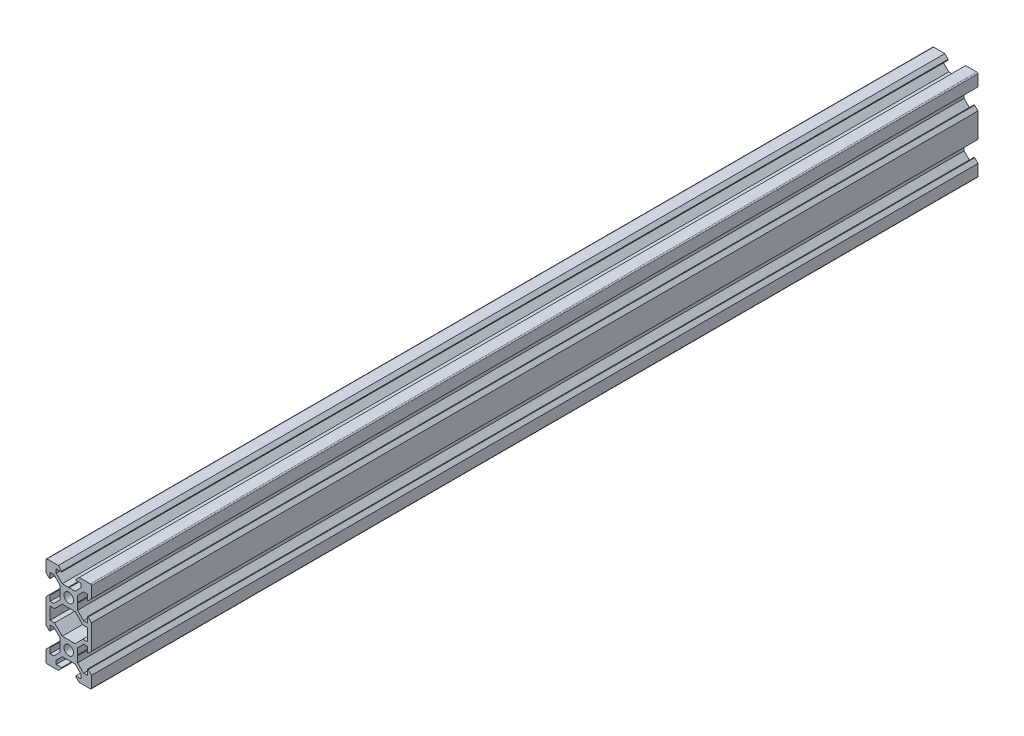
SolidWorks part; units mm, degrees
material "6061-T6 (SS)"
ref_plane "Front Plane" through (0, 0, 0) normal (0, 0, 1) x (1, 0, 0)
ref_plane "Top Plane" through (0, 0, 0) normal (0, 1, 0) x (1, 0, 0)
ref_plane "Right Plane" through (0, 0, 0) normal (1, 0, 0) x (0, 0, -1)
sketch "Sketch1" plane through (0, 0, 0) normal (0, 0, 1) x (1, 0, 0)
  line L0 (0, 0) -> (10, 0) construction
  line L1 (9.5, -20) -> (-9.5, -20)
  line L2 (10, -19.5) -> (10, 19.5)
  line L3 (9.5, 20) -> (-9.5, 20)
  line L4 (-10, -19.5) -> (-10, 19.5)
  line L5 (10, -20) -> (-10, 20) construction
  line L6 (10, 20) -> (-10, -20) construction
  circle A0 centre (0, 10) radius 2.1
  circle A1 centre (0, -10) radius 2.1
  arc A2 (-9.5, -20) -> (-10, -19.5) centre (-9.5, -19.5) cw
  arc A3 (9.5, -20) -> (10, -19.5) centre (9.5, -19.5) ccw
  arc A4 (10, 19.5) -> (9.5, 20) centre (9.5, 19.5) ccw
  arc A5 (-9.5, 20) -> (-10, 19.5) centre (-9.5, 19.5) ccw
  point P0 (0, 0)
  line B0 (0, 10) -> (0, 20) construction
  line B1 (0, 13.69) -> (-0.21, 13.9)
  line B2 (-0.21, 13.9) -> (-2.8393, 13.9)
  line B3 (-2.8393, 13.9) -> (-5.5, 16.5607)
  line B4 (-5.5, 16.5607) -> (-5.5, 18.2)
  line B5 (-5.5, 18.2) -> (-3.125, 18.2)
  line B6 (-3.125, 18.2) -> (-3.125, 18.545)
  line B7 (-3.125, 18.545) -> (-4.58, 20)
  line B8 (-4.58, 20) -> (4.58, 20)
  line B9 (0, 10) -> (-5.9132, 15.9132) construction
  line B10 (3.125, 18.545) -> (4.58, 20)
  line B11 (3.125, 18.2) -> (3.125, 18.545)
  line B12 (5.5, 18.2) -> (3.125, 18.2)
  line B13 (5.5, 16.5607) -> (5.5, 18.2)
  line B14 (2.8393, 13.9) -> (5.5, 16.5607)
  line B15 (0.21, 13.9) -> (2.8393, 13.9)
  line B16 (0, 13.69) -> (0.21, 13.9)
  line B17 (0, 10) -> (-10, 10) construction
  line B18 (-3.69, 10) -> (-3.9, 9.79)
  line B19 (-3.9, 9.79) -> (-3.9, 7.1607)
  line B20 (-3.9, 7.1607) -> (-6.5607, 4.5)
  line B21 (-6.5607, 4.5) -> (-8.2, 4.5)
  line B22 (-8.2, 4.5) -> (-8.2, 6.875)
  line B23 (-8.2, 6.875) -> (-8.545, 6.875)
  line B24 (-8.545, 6.875) -> (-10, 5.42)
  line B25 (-10, 5.42) -> (-10, 14.58)
  line B26 (0, 10) -> (-5.9132, 4.0868) construction
  line B27 (-8.545, 13.125) -> (-10, 14.58)
  line B28 (-8.2, 13.125) -> (-8.545, 13.125)
  line B29 (-8.2, 15.5) -> (-8.2, 13.125)
  line B30 (-6.5607, 15.5) -> (-8.2, 15.5)
  line B31 (-3.9, 12.8393) -> (-6.5607, 15.5)
  line B32 (-3.9, 10.21) -> (-3.9, 12.8393)
  line B33 (-3.69, 10) -> (-3.9, 10.21)
  line B34 (0, -10) -> (-10, -10) construction
  line B35 (-3.69, -10) -> (-3.9, -10.21)
  line B36 (-3.9, -10.21) -> (-3.9, -12.8393)
  line B37 (-3.9, -12.8393) -> (-6.5607, -15.5)
  line B38 (-6.5607, -15.5) -> (-8.2, -15.5)
  line B39 (-8.2, -15.5) -> (-8.2, -13.125)
  line B40 (-8.2, -13.125) -> (-8.545, -13.125)
  line B41 (-8.545, -13.125) -> (-10, -14.58)
  line B42 (-10, -14.58) -> (-10, -5.42)
  line B43 (0, -10) -> (-5.9132, -15.9132) construction
  line B44 (-8.545, -6.875) -> (-10, -5.42)
  line B45 (-8.2, -6.875) -> (-8.545, -6.875)
  line B46 (-8.2, -4.5) -> (-8.2, -6.875)
  line B47 (-6.5607, -4.5) -> (-8.2, -4.5)
  line B48 (-3.9, -7.1607) -> (-6.5607, -4.5)
  line B49 (-3.9, -9.79) -> (-3.9, -7.1607)
  line B50 (-3.69, -10) -> (-3.9, -9.79)
  line B51 (0, -10) -> (0, -20) construction
  line B52 (0, -13.69) -> (0.21, -13.9)
  line B53 (0.21, -13.9) -> (2.8393, -13.9)
  line B54 (2.8393, -13.9) -> (5.5, -16.5607)
  line B55 (5.5, -16.5607) -> (5.5, -18.2)
  line B56 (5.5, -18.2) -> (3.125, -18.2)
  line B57 (3.125, -18.2) -> (3.125, -18.545)
  line B58 (3.125, -18.545) -> (4.58, -20)
  line B59 (4.58, -20) -> (-4.58, -20)
  line B60 (0, -10) -> (5.9132, -15.9132) construction
  line B61 (-3.125, -18.545) -> (-4.58, -20)
  line B62 (-3.125, -18.2) -> (-3.125, -18.545)
  line B63 (-5.5, -18.2) -> (-3.125, -18.2)
  line B64 (-5.5, -16.5607) -> (-5.5, -18.2)
  line B65 (-2.8393, -13.9) -> (-5.5, -16.5607)
  line B66 (-0.21, -13.9) -> (-2.8393, -13.9)
  line B67 (0, -13.69) -> (-0.21, -13.9)
  line B68 (0, -10) -> (10, -10) construction
  line B69 (3.69, -10) -> (3.9, -9.79)
  line B70 (3.9, -9.79) -> (3.9, -7.1607)
  line B71 (3.9, -7.1607) -> (6.5607, -4.5)
  line B72 (6.5607, -4.5) -> (8.2, -4.5)
  line B73 (8.2, -4.5) -> (8.2, -6.875)
  line B74 (8.2, -6.875) -> (8.545, -6.875)
  line B75 (8.545, -6.875) -> (10, -5.42)
  line B76 (10, -5.42) -> (10, -14.58)
  line B77 (0, -10) -> (5.9132, -4.0868) construction
  line B78 (8.545, -13.125) -> (10, -14.58)
  line B79 (8.2, -13.125) -> (8.545, -13.125)
  line B80 (8.2, -15.5) -> (8.2, -13.125)
  line B81 (6.5607, -15.5) -> (8.2, -15.5)
  line B82 (3.9, -12.8393) -> (6.5607, -15.5)
  line B83 (3.9, -10.21) -> (3.9, -12.8393)
  line B84 (3.69, -10) -> (3.9, -10.21)
  line B85 (0, 10) -> (10, 10) construction
  line B86 (3.69, 10) -> (3.9, 10.21)
  line B87 (3.9, 10.21) -> (3.9, 12.8393)
  line B88 (3.9, 12.8393) -> (6.5607, 15.5)
  line B89 (6.5607, 15.5) -> (8.2, 15.5)
  line B90 (8.2, 15.5) -> (8.2, 13.125)
  line B91 (8.2, 13.125) -> (8.545, 13.125)
  line B92 (8.545, 13.125) -> (10, 14.58)
  line B93 (10, 14.58) -> (10, 5.42)
  line B94 (0, 10) -> (5.9132, 15.9132) construction
  line B95 (8.545, 6.875) -> (10, 5.42)
  line B96 (8.2, 6.875) -> (8.545, 6.875)
  line B97 (8.2, 4.5) -> (8.2, 6.875)
  line B98 (6.5607, 4.5) -> (8.2, 4.5)
  line B99 (3.9, 7.1607) -> (6.5607, 4.5)
  line B100 (3.9, 9.79) -> (3.9, 7.1607)
  line B101 (3.69, 10) -> (3.9, 9.79)
  line B102 (-8.2, -2.7) -> (-8.2, 2.7)
  line B103 (-8.2, 2.7) -> (-6.2393, 2.7)
  line B104 (-6.2393, 2.7) -> (-2.8393, 6.1)
  line B105 (-2.8393, 6.1) -> (2.8393, 6.1)
  line B106 (0, 6.1) -> (0, 0) construction
  line B107 (0, 0) -> (-8.2, 0) construction
  line B108 (6.2393, 2.7) -> (2.8393, 6.1)
  line B109 (8.2, 2.7) -> (6.2393, 2.7)
  line B110 (8.2, -2.7) -> (8.2, 2.7)
  line B111 (8.2, -2.7) -> (6.2393, -2.7)
  line B112 (6.2393, -2.7) -> (2.8393, -6.1)
  line B113 (-2.8393, -6.1) -> (2.8393, -6.1)
  line B114 (-6.2393, -2.7) -> (-2.8393, -6.1)
  line B115 (-8.2, -2.7) -> (-6.2393, -2.7)
  line B116 (0, 6.1) -> (0, 10) construction
  line B117 (0, 10) -> (-5.0927, 4.9073) construction
  dimension "D4" = 4.2
  dimension "D5" = 0.5
  dimension "D1" = 20
  dimension "D2" = 40
  dimension "D3" = 20
sketch_block_instance "V Slot 1-4"
sketch_block "V Slot 1" parameters "D1"=10, "D2"=11, "D3"=4.3, "D4"=1.8, "D5"=0.21, "D6"=45, "D7"=9.16, "D8"=1.5, "D9"=6.25
sketch_block_instance "V Slot 1-5"
sketch_block_instance "V Slot 1-6"
sketch_block_instance "V Slot 1-7"
sketch_block_instance "V Slot 1-8"
sketch_block_instance "V Slot 1-9"
sketch_block_instance "Center Cutout 1-1"
sketch_block "Center Cutout 1" parameters "D1"=5.4, "D2"=12.2, "D3"=8.2, "D4"=45, "D5"=10, "D6"=1.5
extrude "Boss-Extrude1" add sketch "Sketch1" along normal blind 390 contours B101 B86 B87 B88 B89 B90 B91 B92 L2 A4 L3 B10 B11 B12 B13 B14 B15 B16 B1 B2 B3 B4 B5 B6 B7 A5 L4 B27 B28 B29 B30 B31 B32 B33 B18 B19 B20 B21 B22 B23 B24 B44 B45 B46 B47 B48 B49 B50 B35
